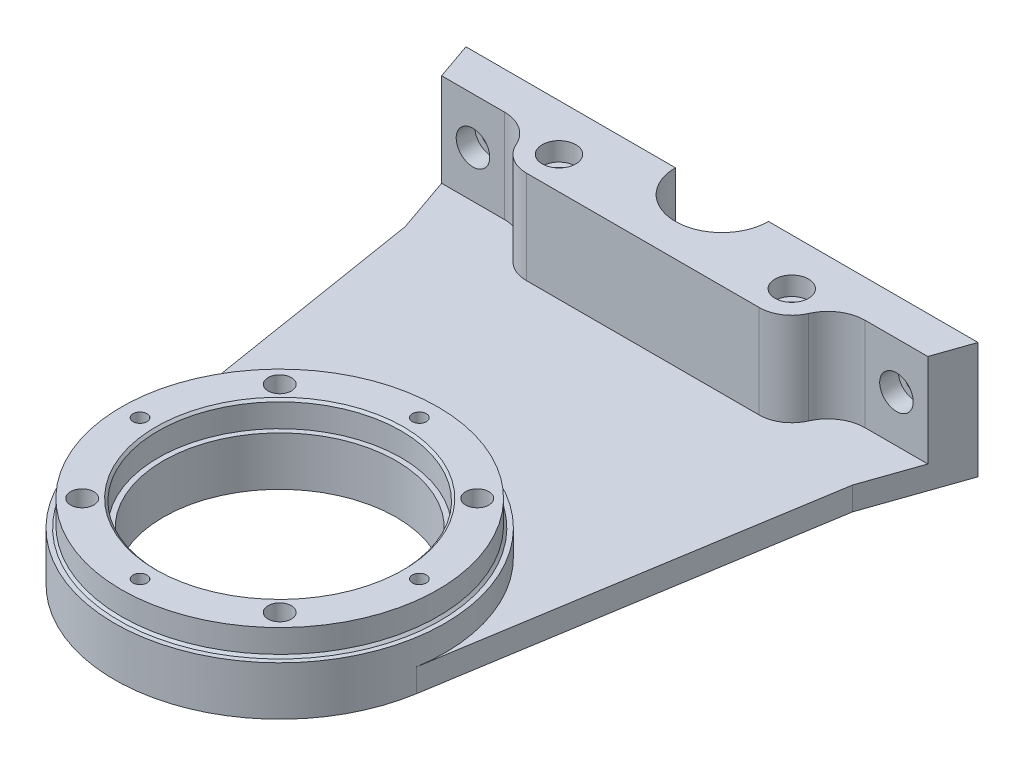
SolidWorks part; units mm, degrees
ref_plane "Front Plane" through (0, 0, 0) normal (0, 0, 1) x (1, 0, 0)
ref_plane "Top Plane" through (0, 0, 0) normal (0, 1, 0) x (1, 0, 0)
ref_plane "Right Plane" through (0, 0, 0) normal (1, 0, 0) x (0, 0, -1)
sketch "Sketch1" plane through (0, 0, 0) normal (0, 1, 0) x (1, 0, 0)
  circle A0 centre (0, 0) radius 34
  circle A1 centre (0, 0) radius 26.1
  dimension "D1" = 68
  dimension "D2" = 52.2
extrude "Boss-Extrude1" add sketch "Sketch1" along normal blind 5.5
sketch "Sketch2" plane through (0, 0, 0) normal (0, -1, 0) x (-1, 0, 0)
  circle A0 centre (0, 0) radius 35.5
  circle A1 centre (0, 0) radius 25
  dimension "D1" = 71
  dimension "D2" = 50
extrude "Boss-Extrude2" add sketch "Sketch2" along normal blind 5.5
sketch "Sketch3" plane through (0, -5.5, 0) normal (0, -1, 0) x (1, 0, 0)
  line L0 (-55, -95) -> (-10, -95)
  line L1 (-55, -95) -> (-48.055, -75)
  line L2 (55, -95) -> (48.055, -75)
  line L3 (-48.055, -75) -> (-35.0471, 5.6525)
  line L4 (48.055, -75) -> (35.0471, 5.6525)
  line L5 (10, -95) -> (55, -95)
  arc A0 (10, -95) -> (-10, -95) centre (0, -95) ccw
  circle A1 centre (0, 0) radius 25 construction
  circle A2 centre (0, 0) radius 35.5 construction
  circle A3 centre (0, 0) radius 25
  arc A4 (35.0471, 5.6525) -> (-35.0471, 5.6525) centre (0, 0) ccw
  circle A5 centre (-25, -85) radius 2.2
  circle A6 centre (25, -85) radius 2.2
  dimension "D9" = 4.4
  dimension "D10" = 20
  dimension "D1" = 95
  dimension "D2" = 96.11
  dimension "D3" = 110
  dimension "D4" = 6.945
  dimension "D5" = 20
  dimension "D6" = 25
  dimension "D7" = 50
  dimension "D8" = 10
extrude "Boss-Extrude3" add sketch "Sketch3" along normal blind 5 contours L3 A4 L4 L2 L5 A0 L0 L1 | A5 | A6 | A3
chamfer "Chamfer1" distance 0.5 angle 45 2 edges at (0, 0, 34) (0, 5.5, 26.1)
sketch "Sketch5" plane through (0, 5.5, 0) normal (0, 1, 0) x (1, 0, 0)
  line L0 (0, 0) -> (0, 30) construction
  line L1 (0, 0) -> (21.2132, 21.2132) construction
  circle A4 centre (21.2132, 21.2132) radius 2.5
  circle A5 centre (0, 30) radius 1.5
  circle A6 centre (30, 0) radius 1.5
  circle A7 centre (0, -30) radius 1.5
  circle A8 centre (-30, 0) radius 1.5
  circle A9 centre (21.2132, -21.2132) radius 2.5
  circle A10 centre (-21.2132, -21.2132) radius 2.5
  circle A11 centre (-21.2132, 21.2132) radius 2.5
  point P12 (0, 0)
  point P22 (0, 0)
  dimension "D1" = 30
  dimension "D3" = 3
  dimension "D6" = 5
  dimension "D2" = 4
  dimension "D4" = 45
  dimension "D5" = 30
  dimension "D7" = 4
extrude "Cut-Extrude1" cut sketch "Sketch5" against normal through all
sketch "Sketch6" plane through (0, -5.5, 0) normal (0, 1, 0) x (1, 0, 0)
  line L0 (55, 95) -> (48.055, 75) construction
  line L1 (10, 95) -> (55, 95) construction
  line L2 (-55, 95) -> (-48.055, 75) construction
  line L3 (-55, 95) -> (-10, 95) construction
  line L4 (55, 95) -> (52.222, 87)
  line L5 (10, 95) -> (55, 95)
  line L6 (-55, 95) -> (-52.222, 87)
  line L7 (-55, 95) -> (-10, 95)
  line L8 (-48.055, 75) -> (48.055, 75)
  line L9 (-52.222, 87) -> (-38.7477, 87)
  line L10 (-25, 78) -> (25, 78)
  line L11 (38.7477, 87) -> (52.222, 87)
  circle A0 centre (25, 85) radius 2.2 construction
  circle A1 centre (-25, 85) radius 2.2 construction
  circle A2 centre (25, 85) radius 2.2
  circle A3 centre (-25, 85) radius 2.2
  arc A4 (-31.4156, 82.2) -> (-25, 78) centre (-25, 85) ccw
  arc A5 (25, 78) -> (31.4156, 82.2) centre (25, 85) ccw
  arc A6 (31.4156, 82.2) -> (38.7477, 87) centre (38.7477, 79) cw
  arc A7 (-38.7477, 87) -> (-31.4156, 82.2) centre (-38.7477, 79) cw
  point P20 (31.7082, 87)
  circle M1 centre (25, 85) radius 2.2
  circle M2 centre (-25, 85) radius 2.2
  line M6 (48.055, 75) -> (55, 95)
  line M7 (55, 95) -> (10, 95)
  arc M8 (10, 95) -> (-10, 95) centre (0, 95) cw
  line M9 (-10, 95) -> (-55, 95)
  line M10 (-55, 95) -> (-48.055, 75)
  dimension "D1" = 14
  dimension "D3" = 8
  dimension "D2" = 8
extrude "Boss-Extrude4" add sketch "Sketch6" along normal blind 20 contours L8 M10 M6 M7 M8 M9 M2 M1
sketch "Sketch7" plane through (0, 14.5, 0) normal (0, 1, 0) x (1, 0, 0)
  circle A0 centre (25, 85) radius 3.6
  circle A1 centre (-25, 85) radius 3.6
  dimension "D1" = 7.2
extrude "Cut-Extrude2" cut sketch "Sketch7" against normal blind 4
sketch "Sketch8" plane through (0, 0, -87) normal (0, 0, 1) x (1, 0, 0)
  line L0 (-52.222, 14.5) -> (-52.222, -5.5) construction
  line L1 (-52.222, 14.5) -> (-38.7477, 14.5) construction
  line L2 (0, 0) -> (0, 23.5197) construction
  circle A0 centre (-45.4849, 4.5) radius 2.2
  circle A1 centre (45.4849, 4.5) radius 2.2
  point P4 (-52.222, 4.5)
  point P7 (-45.4849, 14.5)
  dimension "D1" = 4.4
extrude "Cut-Extrude3" cut sketch "Sketch8" against normal blind 8
sketch "Sketch9" plane through (0, 0, -87) normal (0, 0, 1) x (1, 0, 0)
  circle A0 centre (-45.4849, 4.5) radius 3.6
  circle A1 centre (45.4849, 4.5) radius 3.6
  dimension "D1" = 7.2
extrude "Cut-Extrude4" cut sketch "Sketch9" against normal blind 4
